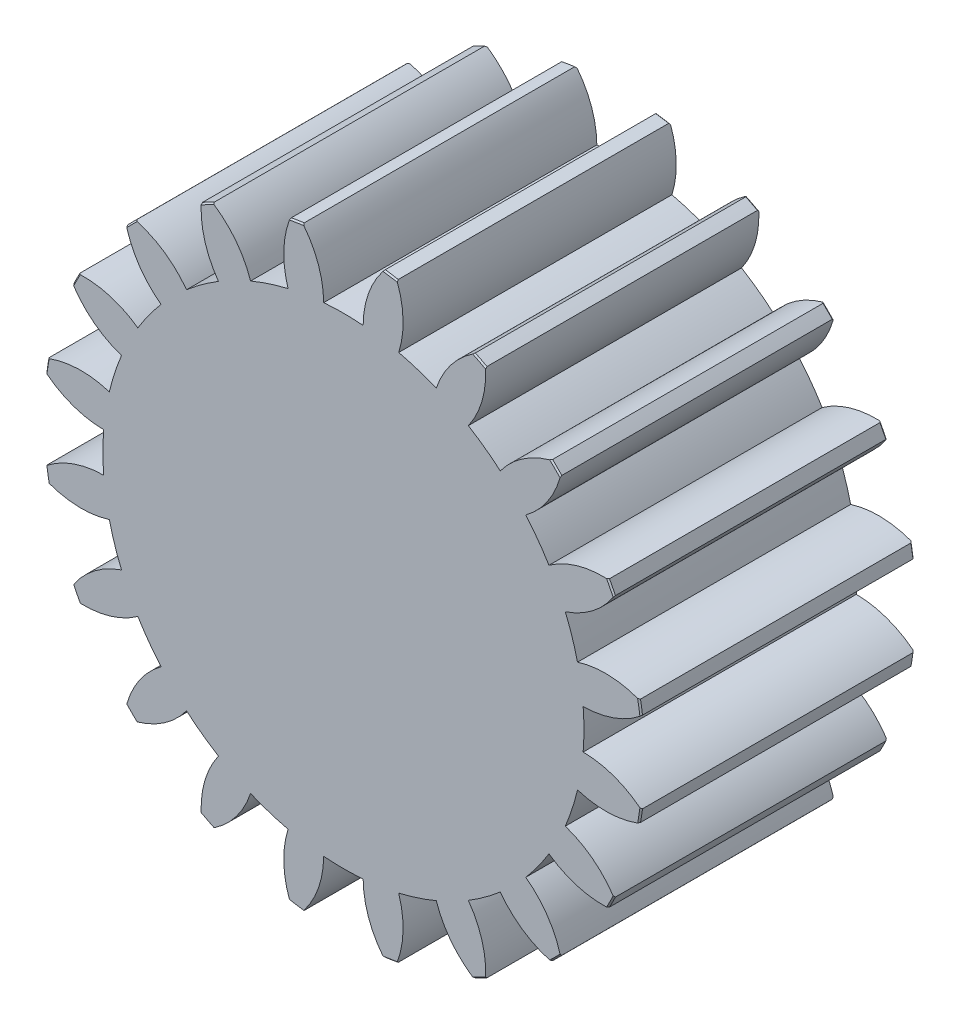
SolidWorks part; units mm, degrees
ref_plane "Front Plane" through (0, 0, 0) normal (0, 0, 1) x (1, 0, 0)
ref_plane "Top Plane" through (0, 0, 0) normal (0, 1, 0) x (1, 0, 0)
ref_plane "Right Plane" through (0, 0, 0) normal (1, 0, 0) x (0, 0, -1)
sketch "Sketch2" plane through (0, 0, 0) normal (0, 0, 1) x (1, 0, 0)
  circle A0 centre (0, 0) radius 20 construction
  circle A1 centre (0, 0) radius 22
  dimension "pitch cirlcle" = 40
  dimension "pitch circle 2" = 44
extrude "Boss-Extrude1" add sketch "Sketch2" along normal mid plane 20
sketch "Sketch3" plane through (0, 0, 10) normal (0, 0, 1) x (1, 0, 0)
  line L0 (0, 0) -> (0, 22) construction
  line L1 (6.7984, 20.9232) -> (0, 0) construction
  line L2 (0, 0) -> (3.4416, 21.7291) construction
  line L3 (0, 0) -> (-1.1551, 17.9629) construction
  line L4 (-1.5692, 19.9383) -> (1.5692, 19.9383) construction
  line L5 (1.5692, 19.9383) -> (4.6689, 19.4474) construction
  line L6 (0, 15.6271) -> (-2.2766, 21.8819) construction
  arc A0 (1.1551, 17.9629) -> (-1.1551, 17.9629) centre (0, 0) ccw
  circle A2 centre (0, 0) radius 22 construction
  circle A3 centre (0, 0) radius 19.75 construction
  arc A4 (-2.6166, 21.8438) -> (-1.1551, 17.9629) centre (-8.2502, 17.5067) cw
  arc A5 (2.6166, 21.8438) -> (1.1551, 17.9629) centre (8.2502, 17.5067) ccw
  circle A6 centre (0, 0) radius 20 construction
  circle A7 centre (0, 0) radius 22 construction
  arc A8 (2.6166, 21.8438) -> (-2.6166, 21.8438) centre (0, 0) ccw
  dimension "angle displacement" = 18
  dimension "dedenum" = 4
  dimension "addendum" = 2.25
  dimension "Pressure Angle" = 20
extrude "Cut-Extrude1" cut sketch "Sketch3" against normal blind 10
fillet "Fillet1" radius 0.6 2 edges at (1.1551, 17.9629, 5) (-1.1551, 17.9629, 5)
chamfer "Chamfer1" distance 0.1 2 edges at (22, 0, -10) (0, -22, 10)
pattern_circular "CirPattern1" count 20 over 360 about axis through (0, 0, 0) along (0, 0, 1) of "Cut-Extrude1", "Fillet1"
sketch "Sketch6" plane through (0, 0, 10) normal (0, 0, 1) x (1, 0, 0)
  line L0 (-2.969, 21.7987) -> (-2.3981, 24.057)
  line L1 (-2.3981, 24.057) -> (2.7785, 23.6602)
  line L2 (2.7785, 23.6602) -> (2.969, 21.7987)
  arc A0 (-1.445, 17.5517) -> (-2.969, 21.7987) centre (-8.2502, 17.5067) ccw
  arc A1 (2.969, 21.7987) -> (1.445, 17.5517) centre (8.2502, 17.5067) ccw
  arc A2 (-2.5466, 21.7514) -> (-2.6166, 21.8438) centre (-8.2502, 17.5067) ccw construction
  arc A3 (2.6166, 21.8438) -> (2.5466, 21.7514) centre (8.2502, 17.5067) ccw construction
  arc A4 (-2.6166, 21.8438) -> (-4.2616, 21.5833) centre (0, 0) ccw construction
  arc A5 (4.2616, 21.5833) -> (2.6166, 21.8438) centre (0, 0) ccw construction
  arc A7 (1.445, 17.5517) -> (-1.445, 17.5517) centre (0, 0) ccw
extrude "Cut-Extrude3" cut sketch "Sketch6" against normal through all
pattern_circular "CirPattern2" count 20 over 360 about axis through (0, 0, 0) along (0, 0, 1) of "Cut-Extrude3"
ref_point "Point1"
equation "\"module\"= 2mm"
equation "\"number of teeth\"= 20"
equation "\"pressure angle\"= 20"
equation "\"pitch cirlcle@Sketch2\"= \"module\" * \"number of teeth\""
equation "\"pitch circle 2@Sketch2\"= \"module\" * ( \"number of teeth\" + 2 )"
equation "\"angle displacement@Sketch3\"= 360 / \"number of teeth\""
equation "\"addendum@Sketch3\"= IIF ( \"module\" >= 1.25 , 2.25 , 2.4 )"
equation "\"Pressure Angle@Sketch3\"= \"pressure angle\""
equation "\"D1@CirPattern1\"= \"number of teeth\""
equation "\"D1@Fillet1\"= 0.3 * \"module\""
equation "\"D1@CirPattern2\"=\"number of teeth\""
